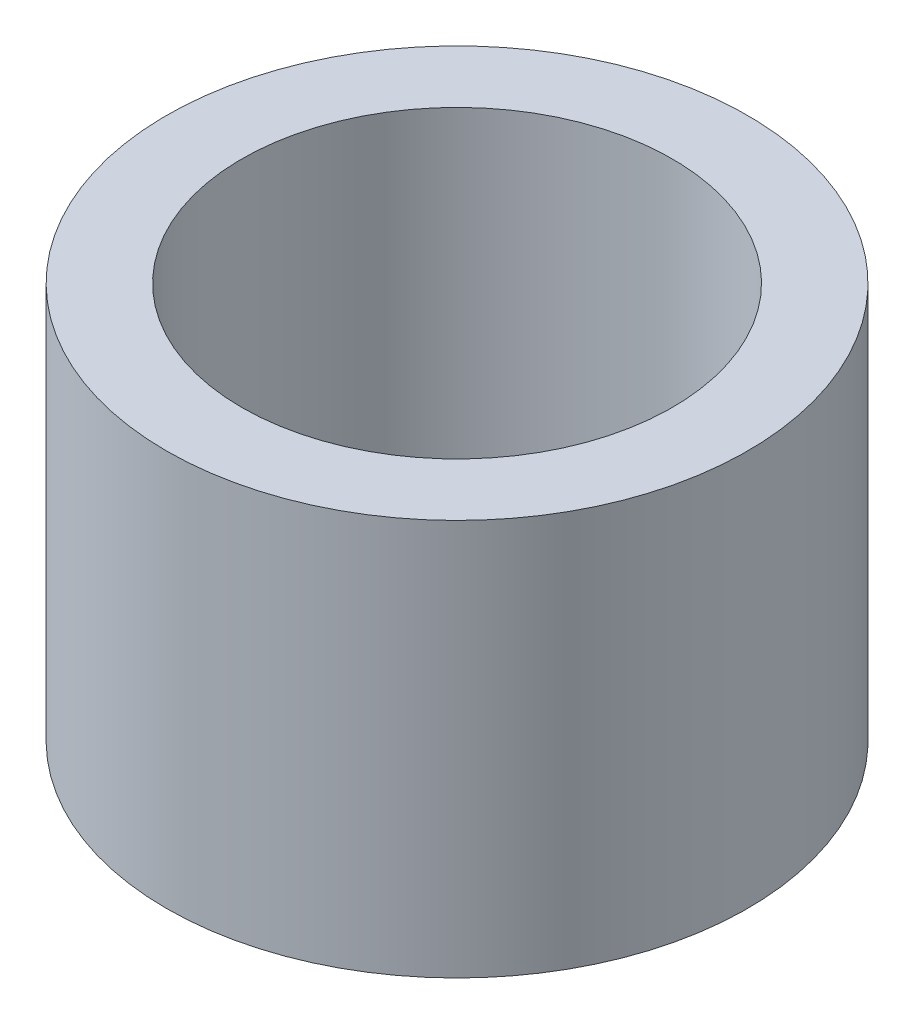
SolidWorks part; units mm, degrees
ref_plane "Спереди" through (0, 0, 0) normal (0, 0, 1) x (1, 0, 0)
ref_plane "Сверху" through (0, 0, 0) normal (0, 1, 0) x (1, 0, 0)
ref_plane "Справа" through (0, 0, 0) normal (1, 0, 0) x (0, 0, -1)
sketch "Sketch1" plane through (0, 0, 0) normal (0, 1, 0) x (1, 0, 0)
  circle A0 centre (0, 0) radius 8.15
  circle A1 centre (0, 0) radius 11
  dimension "D1" = 16.3
  dimension "D2" = 22
extrude "Boss-Extrude1" add sketch "Sketch1" along normal blind 15
